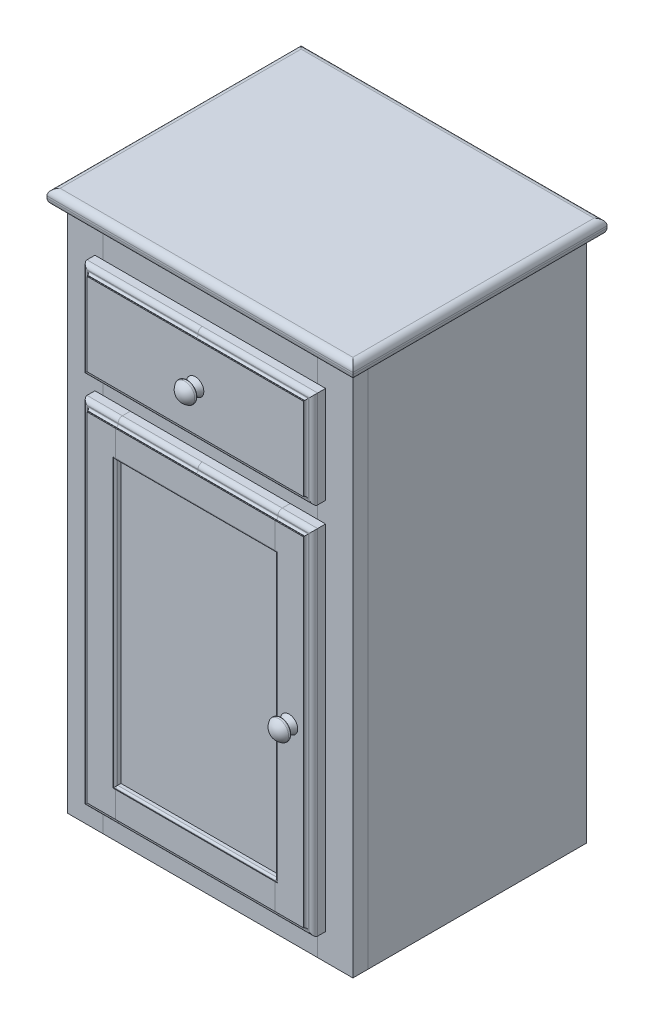
SolidWorks part; units mm, degrees
ref_plane "Front Plane" through (0, 0, 0) normal (0, 0, 1) x (1, 0, 0)
ref_plane "Top Plane" through (0, 0, 0) normal (0, 1, 0) x (1, 0, 0)
ref_plane "Right Plane" through (0, 0, 0) normal (1, 0, 0) x (0, 0, -1)
sketch "Sketch1" plane through (0, 0, 0) normal (1, 0, 0) x (0, 0, -1)
  line L1 (0, 0) -> (-294.64, 0)
  line L2 (0, 0) -> (0, 709.93)
  line L3 (0, 709.93) -> (-294.64, 709.93)
  line L4 (-294.64, 0) -> (-294.64, 709.93)
  dimension "D1" = 294.64
  dimension "D2" = 709.93
extrude "Right Side" add sketch "Sketch1" against normal blind 20.32
sketch "Sketch2" plane through (0, 709.93, 0) normal (0, 1, 0) x (1, 0, 0)
  line L0 (0, 0) -> (0, -294.64) construction
  line L1 (13.97, 13.97) -> (-398.78, 13.97)
  line L2 (13.97, 13.97) -> (13.97, -328.93)
  line L3 (13.97, -328.93) -> (-398.78, -328.93)
  line L4 (-398.78, 13.97) -> (-398.78, -328.93)
  line L5 (-20.32, 0) -> (0, 0) construction
  dimension "D1" = 412.75
  dimension "D2" = 342.9
  dimension "D3" = 13.97
  dimension "D4" = 13.97
extrude "Top" add sketch "Sketch2" along normal blind 20.32 separate body
fillet "Top Router" radius 8.89 8 edges at (13.97, 709.93, 157.48) (-192.405, 709.93, -13.97) (-398.78, 709.93, 157.48) (-192.405, 709.93, 328.93) (13.97, 730.25, 157.48) (-192.405, 730.25, 328.93) (-192.405, 730.25, -13.97) (-398.78, 730.25, 157.48)
sketch "Sketch3" plane through (0, 709.93, 0) normal (0, -1, 0) x (1, 0, 0)
  line L0 (-398.78, -13.97) -> (-398.78, 328.93) construction
  line L1 (-364.49, 294.64) -> (-384.81, 294.64)
  line L2 (-364.49, 294.64) -> (-364.49, 0)
  line L3 (-364.49, 0) -> (-384.81, 0)
  line L4 (-384.81, 294.64) -> (-384.81, 0)
  line L5 (13.97, -13.97) -> (-398.78, -13.97) construction
  dimension "D1" = 20.32
  dimension "D2" = 294.64
  dimension "D3" = 13.97
  dimension "D4" = 13.97
extrude "Left Side" add sketch "Sketch3" along normal blind 709.93 separate body
sketch "Sketch4" plane through (0, 709.93, 0) normal (0, -1, 0) x (1, 0, 0)
  line L1 (-364.49, 0) -> (-20.32, 0)
  line L2 (-364.49, 0) -> (-364.49, 8.89)
  line L3 (-364.49, 8.89) -> (-20.32, 8.89)
  line L4 (-20.32, 0) -> (-20.32, 8.89)
  line L5 (-364.49, 0) -> (-364.49, 294.64) construction
  line L6 (-20.32, 294.64) -> (-20.32, 0) construction
  line L7 (-20.32, 0) -> (0, 0) construction
  dimension "D1" = 8.89
extrude "Back" add sketch "Sketch4" along normal blind 709.93 separate body
sketch "Sketch5" plane through (0, 0, 8.89) normal (0, 0, 1) x (1, 0, 0)
  line L0 (-364.49, 0) -> (-364.49, 709.93) construction
  line L1 (-364.49, 12.7) -> (-20.32, 12.7)
  line L2 (-364.49, 12.7) -> (-364.49, 33.02)
  line L3 (-364.49, 33.02) -> (-20.32, 33.02)
  line L4 (-20.32, 12.7) -> (-20.32, 33.02)
  line L6 (-20.32, 0) -> (-364.49, 0) construction
  line L7 (-20.32, 0) -> (-20.32, 709.93) construction
  dimension "D1" = 20.32
  dimension "D2" = 12.7
extrude "Bottom" add sketch "Sketch5" along normal blind 285.75 separate body
sketch "Sketch6" plane through (0, 0, 8.89) normal (0, 0, 1) x (1, 0, 0)
  line L1 (-316.738, 709.93) -> (-68.072, 709.93)
  line L2 (-316.738, 709.93) -> (-316.738, 689.61)
  line L3 (-316.738, 689.61) -> (-68.072, 689.61)
  line L4 (-68.072, 709.93) -> (-68.072, 689.61)
  line L7 (-364.49, 0) -> (-364.49, 709.93) construction
  line L8 (-316.738, 547.878) -> (-68.072, 547.878)
  line L9 (-316.738, 547.878) -> (-316.738, 527.558)
  line L10 (-316.738, 527.558) -> (-68.072, 527.558)
  line L11 (-68.072, 547.878) -> (-68.072, 527.558)
  line L14 (-20.32, 0) -> (-20.32, 709.93) construction
  line L15 (-20.32, 709.93) -> (-364.49, 709.93) construction
  dimension "D1" = 20.32
  dimension "D2" = 20.32
  dimension "D3" = 141.732
  dimension "D4" = 47.752
  dimension "D5" = 47.752
  dimension "D6" = 47.752
  dimension "D7" = 47.752
extrude "Inside Frame - Back" add sketch "Sketch6" along normal blind 47.752 separate body
sketch "Sketch8" plane through (0, 0, 8.89) normal (0, 0, 1) x (1, 0, 0)
  line L0 (-316.738, 709.93) -> (-316.738, 689.61) construction
  line L1 (-316.738, 689.61) -> (-364.49, 689.61)
  line L2 (-316.738, 689.61) -> (-316.738, 709.93)
  line L3 (-316.738, 709.93) -> (-364.49, 709.93)
  line L4 (-364.49, 689.61) -> (-364.49, 709.93)
  line L5 (-316.738, 547.878) -> (-316.738, 527.558) construction
  line L6 (-68.072, 689.61) -> (-20.32, 689.61)
  line L7 (-68.072, 689.61) -> (-68.072, 709.93)
  line L8 (-68.072, 709.93) -> (-20.32, 709.93)
  line L9 (-20.32, 689.61) -> (-20.32, 709.93)
  line L10 (-316.738, 547.878) -> (-364.49, 547.878)
  line L11 (-316.738, 547.878) -> (-316.738, 527.558)
  line L12 (-316.738, 527.558) -> (-364.49, 527.558)
  line L13 (-364.49, 547.878) -> (-364.49, 527.558)
  line L14 (-364.49, 0) -> (-364.49, 709.93) construction
  line L15 (-68.072, 527.558) -> (-68.072, 547.878) construction
  line L16 (-68.072, 547.878) -> (-20.32, 547.878)
  line L17 (-68.072, 547.878) -> (-68.072, 527.558)
  line L18 (-68.072, 527.558) -> (-20.32, 527.558)
  line L19 (-20.32, 547.878) -> (-20.32, 527.558)
  line L20 (-20.32, 0) -> (-20.32, 709.93) construction
  line L21 (-68.072, 547.878) -> (-316.738, 547.878) construction
  line L22 (-316.738, 527.558) -> (-68.072, 527.558) construction
  line L23 (-316.738, 689.61) -> (-68.072, 689.61) construction
extrude "Inside Frame - Sides" add sketch "Sketch8" along normal blind 285.75 separate body
sketch "Sketch9" plane through (-68.072, 0, 0) normal (-1, 0, 0) x (0, 0, 1)
  line L0 (294.64, 709.93) -> (8.89, 709.93) construction
  line L1 (294.64, 689.61) -> (246.888, 689.61)
  line L2 (294.64, 689.61) -> (294.64, 709.93)
  line L3 (294.64, 709.93) -> (246.888, 709.93)
  line L4 (246.888, 689.61) -> (246.888, 709.93)
  line L5 (294.64, 547.878) -> (8.89, 547.878) construction
  line L6 (294.64, 527.558) -> (246.888, 527.558)
  line L7 (294.64, 527.558) -> (294.64, 547.878)
  line L8 (294.64, 547.878) -> (246.888, 547.878)
  line L9 (246.888, 527.558) -> (246.888, 547.878)
  dimension "D1" = 47.752
  dimension "D2" = 47.752
extrude "Inside Frame - Front" add sketch "Sketch9" along normal up to next (248.666 mm away) separate body
sketch "Sketch10" plane through (0, 709.93, 0) normal (0, -1, 0) x (1, 0, 0)
  line L0 (-20.32, 294.64) -> (0, 294.64) construction
  line L1 (0, 294.64) -> (-47.752, 294.64)
  line L2 (0, 294.64) -> (0, 314.96)
  line L3 (0, 314.96) -> (-47.752, 314.96)
  line L4 (-47.752, 294.64) -> (-47.752, 314.96)
  line L5 (0, 0) -> (0, 294.64) construction
  line L6 (-384.81, 294.64) -> (-337.058, 294.64)
  line L7 (-384.81, 294.64) -> (-384.81, 314.96)
  line L8 (-384.81, 314.96) -> (-337.058, 314.96)
  line L9 (-337.058, 294.64) -> (-337.058, 314.96)
  dimension "D1" = 47.752
  dimension "D2" = 47.752
  dimension "D3" = 20.32
  dimension "D4" = 20.32
extrude "Front - Side Strips" add sketch "Sketch10" along normal blind 709.93 separate body
sketch "Sketch11" plane through (-47.752, 0, 0) normal (-1, 0, 0) x (0, 0, 1)
  line L0 (294.64, 0) -> (294.64, 709.93) construction
  line L1 (314.96, 709.93) -> (294.64, 709.93)
  line L2 (314.96, 709.93) -> (314.96, 662.178)
  line L3 (314.96, 662.178) -> (294.64, 662.178)
  line L4 (294.64, 709.93) -> (294.64, 662.178)
  line L5 (314.96, 0) -> (314.96, 709.93) construction
  line L6 (314.96, 547.878) -> (294.64, 547.878)
  line L7 (314.96, 547.878) -> (314.96, 500.126)
  line L8 (314.96, 500.126) -> (294.64, 500.126)
  line L9 (294.64, 547.878) -> (294.64, 500.126)
  line L10 (314.96, 0) -> (294.64, 0) construction
  line L11 (294.64, 0) -> (314.96, 0)
  line L12 (294.64, 0) -> (294.64, 47.752)
  line L13 (294.64, 47.752) -> (314.96, 47.752)
  line L14 (314.96, 0) -> (314.96, 47.752)
  dimension "D1" = 47.752
  dimension "D2" = 47.752
  dimension "D3" = 114.3
  dimension "D4" = 47.752
extrude "Front - Center Strips" add sketch "Sketch11" along normal up to next (289.306 mm away) separate body
sketch "Sketch12" plane through (0, 0, 314.96) normal (0, 0, 1) x (1, 0, 0)
  line L0 (-337.058, 662.178) -> (-47.752, 662.178) construction
  line L1 (-347.98, 670.433) -> (-36.83, 670.433)
  line L2 (-347.98, 670.433) -> (-347.98, 539.623)
  line L3 (-347.98, 539.623) -> (-36.83, 539.623)
  line L4 (-36.83, 670.433) -> (-36.83, 539.623)
  line L5 (-337.058, 500.126) -> (-47.752, 500.126) construction
  point P4 (-192.405, 670.433)
  point P5 (-192.405, 662.178)
  point P13 (-192.405, 500.126)
  dimension "D1" = 311.15
  dimension "D2" = 130.81
  dimension "D3" = 8.255
extrude "Top Drawer - Front" add sketch "Sketch12" along normal blind 20.32 separate body
sketch "Sketch13" plane through (0, 0, 294.64) normal (0, 0, -1) x (-1, 0, 0)
  line L0 (20.32, 568.198) -> (47.752, 568.198)
  line L1 (47.752, 0) -> (47.752, 709.93) construction
  line L2 (47.752, 568.198) -> (47.752, 555.498)
  line L3 (47.752, 555.498) -> (68.072, 555.498)
  line L4 (68.072, 555.498) -> (68.072, 547.878)
  line L5 (68.072, 547.878) -> (20.32, 547.878)
  line L6 (20.32, 547.878) -> (68.072, 547.878) construction
  line L7 (20.32, 547.878) -> (20.32, 568.198)
  line L8 (20.32, 709.93) -> (20.32, 0) construction
  line L9 (364.49, 547.878) -> (316.738, 547.878)
  line L10 (316.738, 547.878) -> (316.738, 555.498)
  line L11 (316.738, 555.498) -> (337.058, 555.498)
  line L12 (337.058, 0) -> (337.058, 709.93) construction
  line L13 (337.058, 555.498) -> (337.058, 568.198)
  line L14 (337.058, 568.198) -> (364.49, 568.198)
  line L15 (364.49, 568.198) -> (364.49, 547.878)
  line L16 (364.49, 0) -> (364.49, 709.93) construction
  dimension "D1" = 20.32
  dimension "D2" = 7.62
  dimension "D3" = 20.32
  dimension "D4" = 7.62
extrude "Top Drawer - Rails" add sketch "Sketch13" along normal blind 285.75 separate body
sketch "Sketch14" plane through (0, 555.498, 0) normal (0, 1, 0) x (1, 0, 0)
  line L0 (-334.518, -14.478) -> (-334.518, -8.89)
  line L1 (-337.058, -8.89) -> (-316.738, -8.89) construction
  line L2 (-334.518, -8.89) -> (-50.292, -8.89)
  line L3 (-337.058, -314.96) -> (-47.752, -314.96) construction
  line L4 (-50.292, -8.89) -> (-50.292, -14.478)
  line L5 (-50.292, -14.478) -> (-61.468, -14.478)
  line L6 (-61.468, -14.478) -> (-61.468, -20.066)
  line L7 (-61.468, -20.066) -> (-323.342, -20.066)
  line L8 (-323.342, -20.066) -> (-323.342, -14.478)
  line L9 (-323.342, -14.478) -> (-334.518, -14.478)
  line L10 (-334.518, -314.96) -> (-50.292, -314.96)
  line L11 (-50.292, -314.96) -> (-50.292, -309.372)
  line L12 (-50.292, -309.372) -> (-61.468, -309.372)
  line L13 (-61.468, -309.372) -> (-61.468, -303.784)
  line L14 (-61.468, -303.784) -> (-323.342, -303.784)
  line L15 (-323.342, -303.784) -> (-323.342, -309.372)
  line L16 (-323.342, -309.372) -> (-334.518, -309.372)
  line L17 (-334.518, -309.372) -> (-334.518, -314.96)
  line L18 (-47.752, -8.89) -> (-47.752, -294.64) construction
  line L19 (-337.058, -8.89) -> (-337.058, -294.64) construction
  dimension "D1" = 11.176
  dimension "D2" = 11.176
  dimension "D3" = 5.588
  dimension "D4" = 11.176
  dimension "D5" = 11.176
  dimension "D6" = 5.588
  dimension "D7" = 11.176
  dimension "D8" = 11.176
  dimension "D9" = 2.54
  dimension "D10" = 2.54
  dimension "D11" = 2.54
  dimension "D12" = 2.54
extrude "Top Drawer - Font / Back" add sketch "Sketch14" along normal blind 107.95 separate body
sketch "Sketch15" plane through (0, 555.498, 0) normal (0, 1, 0) x (1, 0, 0)
  line L0 (-61.468, -14.478) -> (-50.292, -14.478) construction
  line L2 (-334.518, -14.478) -> (-323.342, -14.478)
  line L3 (-334.518, -14.478) -> (-334.518, -309.372)
  line L5 (-334.518, -309.372) -> (-323.342, -309.372)
  line L6 (-323.342, -14.478) -> (-323.342, -309.372)
  line L8 (-50.292, -14.478) -> (-61.468, -14.478)
  line L9 (-50.292, -14.478) -> (-50.292, -309.372)
  line L10 (-50.292, -309.372) -> (-61.468, -309.372)
  line L11 (-61.468, -14.478) -> (-61.468, -309.372)
  line L12 (-61.468, -20.066) -> (-61.468, -14.478) construction
  line L13 (-50.292, -14.478) -> (-50.292, -8.89) construction
  line L14 (-50.292, -309.372) -> (-61.468, -309.372) construction
extrude "Top Drawer - Sides" add sketch "Sketch15" along normal blind 107.95 separate body
ref_plane "Top Drawer Plane" through (0, 0, 309.372) normal (0, 0, 1) x (1, 0, 0)
sketch "Sketch17" plane through (0, 0, 309.372) normal (0, 0, 1) x (1, 0, 0)
  line L0 (-347.98, 670.433) -> (-347.98, 539.623) construction
  line L1 (-328.93, 569.595) -> (-55.88, 569.595)
  line L2 (-328.93, 569.595) -> (-328.93, 561.975)
  line L3 (-328.93, 561.975) -> (-55.88, 561.975)
  line L4 (-55.88, 569.595) -> (-55.88, 561.975)
  line L5 (-36.83, 539.623) -> (-36.83, 670.433) construction
  line L7 (-347.98, 539.623) -> (-36.83, 539.623) construction
  dimension "D1" = 19.05
  dimension "D2" = 19.05
  dimension "D3" = 7.62
  dimension "D4" = 22.352
extrude "Top Drawer - Bottom Cuts" cut sketch "Sketch17" against normal blind 294.894
sketch "Sketch18" plane through (0, 0, 309.372) normal (0, 0, 1) x (1, 0, 0)
  line L1 (-328.93, 569.595) -> (-55.88, 569.595)
  line L2 (-328.93, 569.595) -> (-328.93, 561.975)
  line L3 (-328.93, 561.975) -> (-55.88, 561.975)
  line L4 (-55.88, 569.595) -> (-55.88, 561.975)
  line L6 (-347.98, 670.433) -> (-347.98, 539.623) construction
  line L8 (-36.83, 539.623) -> (-36.83, 670.433) construction
  line L9 (-347.98, 539.623) -> (-36.83, 539.623) construction
  dimension "D1" = 19.05
  dimension "D2" = 19.05
  dimension "D3" = 7.62
  dimension "D4" = 22.352
extrude "Top Drawer - Bottom" add sketch "Sketch18" against normal blind 294.894 separate body
ref_plane "Top Drawer - Knob Plane" through (-192.405, 0, 0) normal (1, 0, 0) x (0, 0, -1)
sketch "Sketch19" plane through (-192.405, 0, 0) normal (1, 0, 0) x (0, 0, -1)
  line L0 (-314.96, 670.433) -> (-325.6655, 670.433)
  line L1 (-335.28, 670.433) -> (-314.96, 670.433) construction
  line L2 (-334.01, 661.2506) -> (-334.01, 660.7426)
  line L3 (-314.96, 686.1426) -> (-340.36, 686.1426)
  line L4 (-340.36, 660.7426) -> (-340.36, 686.1426)
  line L5 (-334.01, 660.7426) -> (-340.36, 660.7426)
  line L6 (-314.96, 670.433) -> (-314.96, 686.1426)
  line L7 (-335.28, 539.623) -> (-335.28, 670.433) construction
  line L8 (-331.47, 663.7906) -> (-331.47, 664.6285)
  arc A0 (-325.6655, 670.433) -> (-331.47, 664.6285) centre (-325.6655, 664.6285) ccw
  arc A1 (-331.47, 663.7906) -> (-334.01, 661.2506) centre (-334.01, 663.7906) cw
  dimension "D5" = 5.8045
  dimension "D6" = 2.54
  dimension "D1" = 25.4
  dimension "D2" = 25.4
  dimension "D3" = 0.508
  dimension "D4" = 1.27
  dimension "D7" = 0.8379
sketch "Sketch20" plane through (0, 0, 335.28) normal (0, 0, 1) x (1, 0, 0)
  line L0 (-36.83, 670.433) -> (-347.98, 670.433) construction
  line L1 (-36.83, 539.623) -> (-36.83, 670.433) construction
  line L2 (-347.98, 670.433) -> (-347.98, 539.623) construction
  line L3 (-347.98, 539.623) -> (-36.83, 539.623) construction
  line L4 (-36.83, 670.433) -> (-347.98, 670.433)
  line L5 (-36.83, 539.623) -> (-36.83, 670.433)
  line L6 (-347.98, 670.433) -> (-347.98, 539.623)
  line L7 (-347.98, 539.623) -> (-36.83, 539.623)
sweep "Top Drawer - Router" cut profiles "Sketch19" path "Sketch20"
sketch "Sketch23" plane through (-192.405, 0, 0) normal (1, 0, 0) x (0, 0, -1)
  line L0 (-335.28, 604.901) -> (-357.299, 604.901)
  line L1 (-335.28, 660.7426) -> (-335.28, 549.3134) construction
  line L2 (-335.28, 616.5339) -> (-335.28, 604.901)
  line L4 (-325.6655, 670.433) -> (-314.96, 670.433) construction
  arc A0 (-357.299, 604.901) -> (-349.3947, 618.3441) centre (-341.9153, 604.901) cw
  arc A1 (-349.3947, 618.3441) -> (-345.34, 616.656) centre (-348.0341, 615.8986) cw
  arc A2 (-345.34, 616.656) -> (-344.9497, 613.8254) centre (-355.4082, 613.8254) cw
  arc A3 (-344.9497, 613.8254) -> (-343.4089, 612.6913) centre (-343.7619, 613.8254) ccw
  arc A4 (-343.4089, 612.6913) -> (-335.28, 616.5339) centre (-353.0035, 643.5078) ccw
  dimension "D1" = 2.7985
  dimension "D2" = 15.3837
  dimension "D3" = 8.1289
  dimension "D4" = 1.1877
  dimension "D5" = 32.2755
  dimension "D6" = 11.6329
  dimension "D7" = 65.532
  dimension "D8" = 22.019
  dimension "D9" = 10.06
  dimension "D10" = 1.5408
  dimension "D11" = 14.1147
revolve "Top Drawer - Knob" add sketch "Sketch23" angle 360 about L0
sketch "Sketch24" plane through (0, 0, 314.96) normal (0, 0, 1) x (1, 0, 0)
  line L0 (-36.83, 539.623) -> (-36.83, 670.433) construction
  line L1 (-36.83, 512.064) -> (-84.582, 512.064)
  line L2 (-36.83, 512.064) -> (-36.83, 35.814)
  line L3 (-36.83, 35.814) -> (-84.582, 35.814)
  line L4 (-84.582, 512.064) -> (-84.582, 35.814)
  line L5 (-337.058, 500.126) -> (-47.752, 500.126) construction
  line L6 (-347.98, 670.433) -> (-347.98, 539.623) construction
  line L7 (-300.228, 512.064) -> (-347.98, 512.064)
  line L8 (-300.228, 512.064) -> (-300.228, 35.814)
  line L9 (-300.228, 35.814) -> (-347.98, 35.814)
  line L10 (-347.98, 512.064) -> (-347.98, 35.814)
  dimension "D1" = 47.752
  dimension "D2" = 476.25
  dimension "D3" = 11.938
  dimension "D4" = 47.752
extrude "Bottom Door - Sides" add sketch "Sketch24" along normal blind 20.32 separate body
sketch "Sketch25" plane through (0, 0, 314.96) normal (0, 0, 1) x (1, 0, 0)
  line L0 (-84.582, 512.064) -> (-84.582, 35.814) construction
  line L1 (-300.228, 512.064) -> (-84.582, 512.064)
  line L2 (-300.228, 512.064) -> (-300.228, 464.312)
  line L3 (-300.228, 464.312) -> (-84.582, 464.312)
  line L4 (-84.582, 512.064) -> (-84.582, 464.312)
  line L5 (-300.228, 35.814) -> (-300.228, 512.064) construction
  line L6 (-84.582, 35.814) -> (-300.228, 35.814)
  line L7 (-84.582, 35.814) -> (-84.582, 83.566)
  line L8 (-84.582, 83.566) -> (-300.228, 83.566)
  line L9 (-300.228, 35.814) -> (-300.228, 83.566)
  line L13 (-36.83, 512.064) -> (-84.582, 512.064) construction
  line L14 (-84.582, 35.814) -> (-36.83, 35.814) construction
  dimension "D1" = 47.752
  dimension "D2" = 47.752
  dimension "D3" = 215.646
  dimension "D4" = 215.646
extrude "Bottom Door - Centers" add sketch "Sketch25" along normal blind 20.32 separate body
ref_plane "Bottom Door - Plane" through (0, 0, 325.12) normal (0, 0, 1) x (1, 0, 0)
sketch "Sketch26" plane through (0, 0, 325.12) normal (0, 0, 1) x (1, 0, 0)
  line L0 (-300.228, 35.814) -> (-300.228, 512.064) construction
  line L1 (-312.928, 477.012) -> (-71.882, 477.012)
  line L2 (-312.928, 477.012) -> (-312.928, 70.866)
  line L3 (-312.928, 70.866) -> (-71.882, 70.866)
  line L4 (-71.882, 477.012) -> (-71.882, 70.866)
  line L5 (-84.582, 512.064) -> (-84.582, 35.814) construction
  line L6 (-300.228, 464.312) -> (-84.582, 464.312) construction
  line L7 (-84.582, 83.566) -> (-300.228, 83.566) construction
  dimension "D2" = 12.7
  dimension "D3" = 12.7
  dimension "D4" = 12.7
  dimension "D5" = 12.7
extrude "Bottom Door - Panel Cuts" cut sketch "Sketch26" against normal blind 2.54 and the other way blind 2.54
sketch "Sketch27" plane through (0, 0, 325.12) normal (0, 0, 1) x (1, 0, 0)
  line L1 (-312.928, 477.012) -> (-71.882, 477.012)
  line L2 (-312.928, 477.012) -> (-312.928, 70.866)
  line L3 (-312.928, 70.866) -> (-71.882, 70.866)
  line L4 (-71.882, 477.012) -> (-71.882, 70.866)
  line L8 (-300.228, 464.312) -> (-84.582, 464.312) construction
  line L9 (-300.228, 35.814) -> (-300.228, 512.064) construction
  line L10 (-84.582, 512.064) -> (-84.582, 35.814) construction
  line L11 (-84.582, 83.566) -> (-300.228, 83.566) construction
  dimension "D1" = 12.7
  dimension "D2" = 12.7
  dimension "D3" = 12.7
  dimension "D4" = 12.7
extrude "Bottom Door - Panel" add sketch "Sketch27" along normal blind 2.54 and the other way blind 2.54 separate body
sketch "Sketch22" plane through (-192.405, 0, 0) normal (1, 0, 0) x (0, 0, -1)
  line L0 (-314.96, 512.064) -> (-325.6655, 512.064)
  line L1 (-334.01, 502.8816) -> (-334.01, 502.3736)
  line L2 (-314.96, 527.7736) -> (-340.36, 527.7736)
  line L3 (-340.36, 502.3736) -> (-340.36, 527.7736)
  line L4 (-334.01, 502.3736) -> (-340.36, 502.3736)
  line L5 (-314.96, 512.064) -> (-314.96, 527.7736)
  line L6 (-331.47, 505.4216) -> (-331.47, 506.2595)
  line L7 (-314.96, 0) -> (-314.96, 709.93) construction
  line L9 (-335.28, 512.064) -> (-314.96, 512.064) construction
  arc A0 (-325.6655, 512.064) -> (-331.47, 506.2595) centre (-325.6655, 506.2595) ccw
  arc A1 (-331.47, 505.4216) -> (-334.01, 502.8816) centre (-334.01, 505.4216) cw
  dimension "D4" = 2.54
  dimension "D5" = 5.8045
  dimension "D1" = 25.4
  dimension "D2" = 25.4
  dimension "D3" = 0.508
  dimension "D6" = 10.7055
  dimension "D7" = 0.8379
sketch "Sketch21" plane through (0, 0, 335.28) normal (0, 0, 1) x (1, 0, 0)
  line L4 (-36.83, 512.064) -> (-347.98, 512.064)
  line L5 (-347.98, 512.064) -> (-347.98, 35.814)
  line L6 (-36.83, 35.814) -> (-36.83, 512.064)
  line L7 (-347.98, 35.814) -> (-36.83, 35.814)
  line L8 (0, 0) -> (-47.752, 0) construction
  line L9 (0, 0) -> (0, 709.93) construction
  dimension "D1" = 311.15
  dimension "D2" = 476.25
  dimension "D3" = 35.814
  dimension "D4" = 36.83
sweep "Bottom Door - Router Outside" cut profiles "Sketch22" path "Sketch21"
ref_plane "Bottom Door - Knob Plane" through (-65.786, 0, 0) normal (1, 0, 0) x (0, 0, -1)
sketch "Sketch28" plane through (-65.786, 0, 0) normal (1, 0, 0) x (0, 0, -1)
  line L0 (-335.28, 273.939) -> (-357.299, 273.939)
  line L2 (-335.28, 285.5719) -> (-335.28, 273.939)
  line L3 (-325.6655, 35.814) -> (-314.96, 35.814) construction
  arc A0 (-357.299, 273.939) -> (-349.3947, 287.3821) centre (-341.9153, 273.939) cw
  arc A1 (-349.3947, 287.3821) -> (-345.34, 285.694) centre (-348.0341, 284.9366) cw
  arc A2 (-345.34, 285.694) -> (-344.9497, 282.8634) centre (-355.4082, 282.8634) cw
  arc A3 (-344.9497, 282.8634) -> (-343.4089, 281.7293) centre (-343.7619, 282.8634) ccw
  arc A4 (-343.4089, 281.7293) -> (-335.28, 285.5719) centre (-353.0035, 312.5458) ccw
  dimension "D1" = 2.7985
  dimension "D2" = 15.3837
  dimension "D3" = 8.1289
  dimension "D4" = 1.1877
  dimension "D5" = 32.2755
  dimension "D6" = 11.6329
  dimension "D7" = 238.125
  dimension "D8" = 22.019
  dimension "D9" = 10.06
  dimension "D10" = 1.5408
  dimension "D11" = 14.1147
revolve "Bottom Door - Knob" add sketch "Sketch28" angle 360 about L0
sketch "Sketch29" plane through (-192.405, 0, 0) normal (1, 0, 0) x (0, 0, -1)
  line L0 (-334.645, 467.487) -> (-335.28, 467.487)
  line L1 (-335.28, 467.487) -> (-342.9858, 467.487)
  line L2 (-342.9858, 467.487) -> (-342.9858, 454.787)
  line L3 (-342.9858, 454.787) -> (-327.66, 454.787)
  line L4 (-327.66, 454.787) -> (-327.66, 464.312)
  line L5 (-327.66, 464.312) -> (-332.105, 464.312)
  line L6 (-334.645, 466.852) -> (-334.645, 467.487)
  line L7 (-327.66, 477.012) -> (-327.66, 70.866) construction
  line L8 (-335.28, 464.312) -> (-327.66, 464.312) construction
  line L9 (-335.28, 45.5044) -> (-335.28, 502.3736) construction
  arc A0 (-332.105, 464.312) -> (-334.645, 466.852) centre (-332.105, 466.852) cw
  dimension "D5" = 2.54
  dimension "D1" = 0.635
  dimension "D2" = 0
  dimension "D3" = 0
  dimension "D4" = 0
  dimension "D6" = 0.635
  dimension "D7" = 15.3258
  dimension "D8" = 12.7
sketch "Sketch31" plane through (0, 0, 335.28) normal (0, 0, 1) x (1, 0, 0)
  line L0 (-300.228, 464.312) -> (-84.582, 464.312)
  line L1 (-84.582, 464.312) -> (-84.582, 83.566)
  line L2 (-84.582, 83.566) -> (-300.228, 83.566)
  line L3 (-300.228, 83.566) -> (-300.228, 464.312)
sweep "Bottom Door - Router Inside" cut profiles "Sketch29" path "Sketch31"
